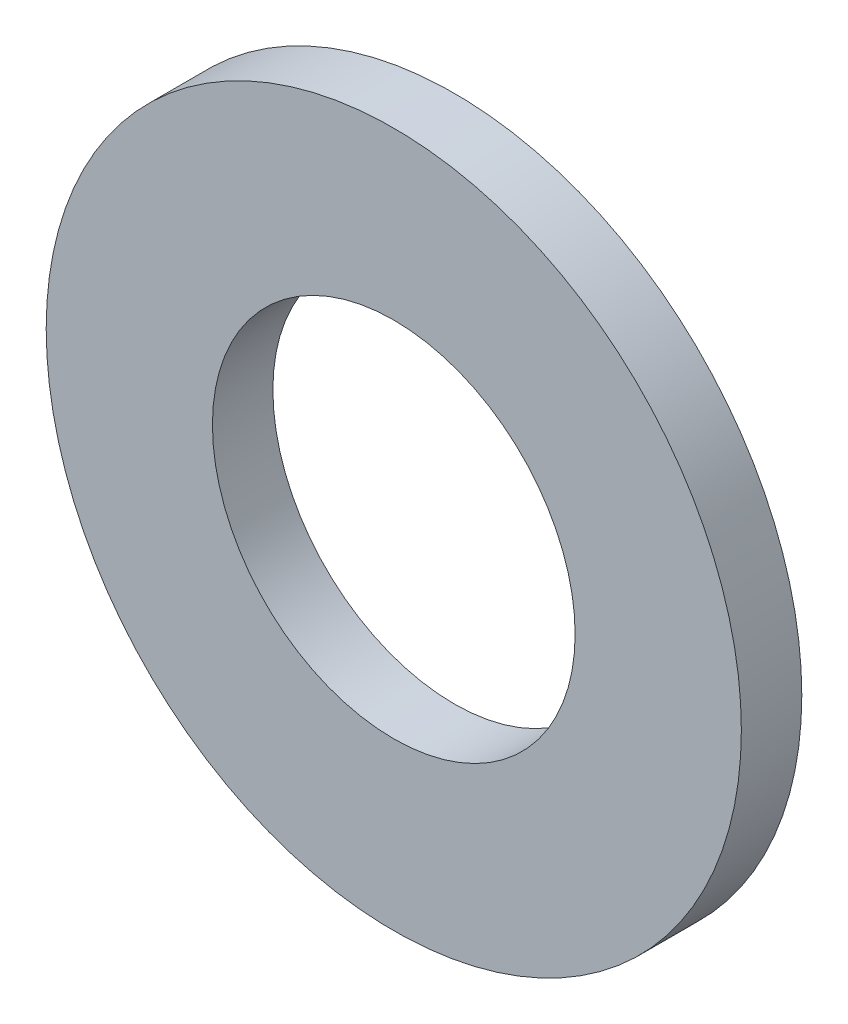
SolidWorks part; units mm, degrees
ref_plane "Front Plane" through (0, 0, 0) normal (0, 0, 1) x (1, 0, 0)
ref_plane "Top Plane" through (0, 0, 0) normal (0, 1, 0) x (1, 0, 0)
ref_plane "Right Plane" through (0, 0, 0) normal (1, 0, 0) x (0, 0, -1)
sketch "Sketch1" plane through (0, 0, 0) normal (0, 0, 1) x (1, 0, 0)
  circle A0 centre (0, 0) radius 6
  circle A1 centre (0, 0) radius 11.5
  dimension "D1" = 12
  dimension "D2" = 23
extrude "Boss-Extrude1" add sketch "Sketch1" along normal blind 2
